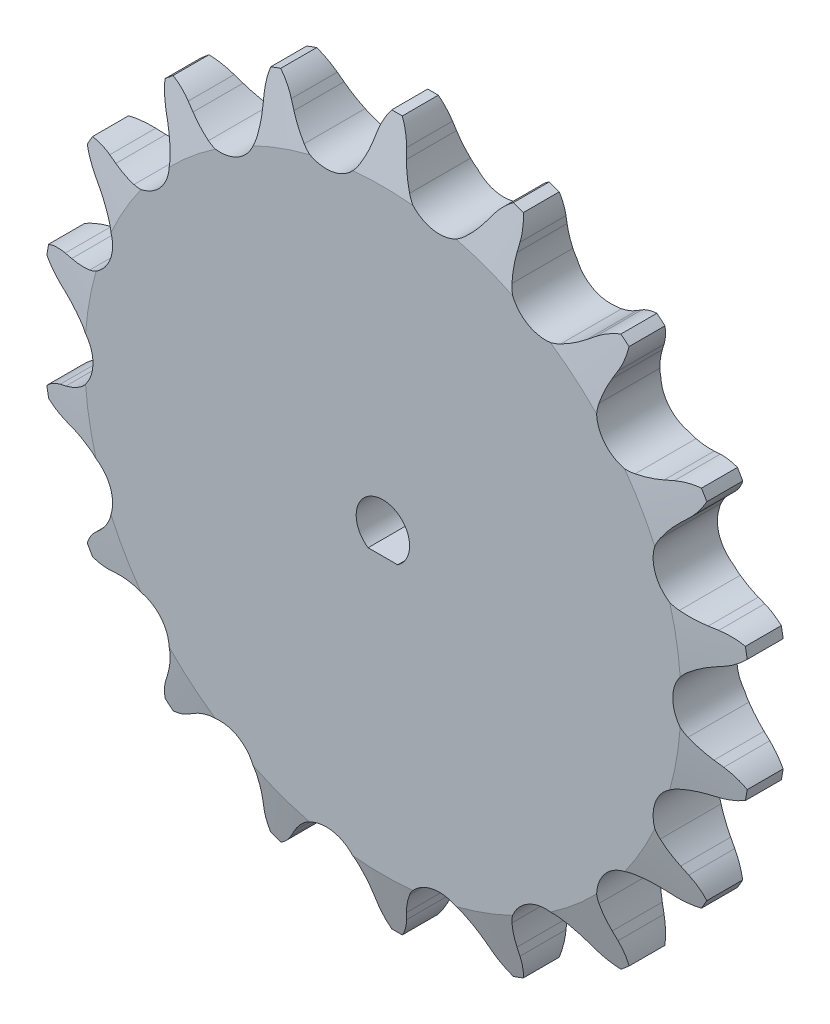
SolidWorks part; units mm, degrees
ref_plane "Front Plane" through (0, 0, 0) normal (0, 0, 1) x (1, 0, 0)
ref_plane "Top Plane" through (0, 0, 0) normal (0, 1, 0) x (1, 0, 0)
ref_plane "Right Plane" through (0, 0, 0) normal (1, 0, 0) x (0, 0, -1)
sketch "Sketch0" plane through (0, 0, 0) normal (0, 0, 1) x (1, 0, 0)
  line L0 (6.35, -36.0126) -> (0, 0) construction
  line L1 (0, 0) -> (18.2841, -31.669) construction
  line L2 (0, 0) -> (-6.35, -36.0126) construction
  line L3 (6.35, -36.0126) -> (18.2841, -31.669) construction
  line L4 (6.35, -36.0126) -> (-6.35, -36.0126) construction
  line L5 (11.3039, -35.8321) -> (10.78, -35.0389)
  line L6 (6.35, -36.0126) -> (0, -37.1323) construction
  line L7 (1.6331, -37.5373) -> (1.8541, -36.6128)
  line L8 (0, -36.0126) -> (0, -39.8226) construction
  line L9 (9.0227, -33.0094) -> (2.1353, -40.7487) construction
  line L10 (0, 0) -> (0, -36.0126) construction
  line L11 (10.78, -35.0389) -> (2.1353, -40.7487) construction
  line L12 (0, -39.8226) -> (0, -40.5391) construction
  line L13 (16.7756, -32.218) -> (11.3039, -35.8321) construction
  circle A0 centre (0, 0) radius 39.8226 construction
  circle A1 centre (0, 0) radius 36.5682 construction
  arc A2 (-5.6013, -42.514) -> (19.8041, -38.0343) centre (0, 0) ccw
  circle A3 centre (0, 0) radius 40.5391 construction
  circle A4 centre (6.35, -36.0126) radius 3.9624 construction
  arc A7 (9.0227, -33.0094) -> (2.8113, -34.1046) centre (6.35, -36.0126) ccw
  circle A8 centre (6.35, -36.0126) radius 4.0203 construction
  arc A9 (11.3039, -35.8321) -> (19.8041, -38.0343) centre (16.7756, -32.218) ccw
  arc A10 (10.78, -35.0389) -> (9.0227, -33.0094) centre (2.1353, -40.7487) ccw
  arc A11 (1.6331, -37.5373) -> (-5.6013, -42.514) centre (-4.7447, -36.0126) cw
  arc A12 (1.8541, -36.6128) -> (2.8113, -34.1046) centre (11.9303, -39.0215) cw
  dimension "D1" = 4.0203
  dimension "R" = 4.0203
sketch "Sketch1" plane through (0, 0, 0) normal (1, 0, 0) x (0, 0, -1)
  line L0 (3.6068, 0) -> (-3.6068, 0)
  line L1 (-3.6068, 0) -> (-3.6068, 33.4726)
  line L2 (-3.6068, 33.4726) -> (-2.0193, 39.8226)
  line L3 (-2.0193, 39.8226) -> (2.0193, 39.8226)
  line L4 (2.0193, 39.8226) -> (3.6068, 33.4726)
  line L5 (3.6068, 33.4726) -> (3.6068, 0)
  line L7 (0, 39.8226) -> (0, 0) construction
  line L8 (-3.6068, 33.4726) -> (3.6068, 33.4726) construction
  line L9 (0, 39.8226) -> (0, -39.8226) construction
  line L10 (-3.6068, 33.4726) -> (-3.6068, 39.8226) construction
  line L11 (-3.6068, 39.8226) -> (-2.0193, 39.8226) construction
  line L12 (2.0193, 39.8226) -> (3.6068, 39.8226) construction
  line L13 (3.6068, 39.8226) -> (3.6068, 33.4726) construction
revolve "Revolve1" add sketch "Sketch1" angle 360 mid plane about L0
extrude "Cut-Extrude1" cut sketch "Sketch0" against normal through all and the other way through all
pattern_circular "CirPattern1" count 18 over 360 about axis through (0, 0, 0) along (0, 0, 1) of "Cut-Extrude1"
sketch "Sketch2" plane through (0, 0, 0) normal (0, 0, 1) x (1, 0, 0)
  circle A0 centre (0, 0) radius 7.9375 construction
  circle A1 centre (0, 0) radius 30.1625
  circle A2 centre (0, 0) radius 39.878 construction
  dimension "Bore" = 15.875
  dimension "Hub Dia." = 60.325
  dimension "OD" = 79.756
sketch "Sketch3" plane through (0, 0, 0) normal (0, 0, 1) x (1, 0, 0)
  line L0 (-1.6583, -2.5) -> (1.6583, -2.5)
  arc A1 (1.6583, -2.5) -> (-1.6583, -2.5) centre (0, 0) ccw
  circle A2 centre (0, 0) radius 39.878 construction
  circle A3 centre (0, 0) radius 39.878
  dimension "D1" = 6
  dimension "D2" = 2.5
extrude "Cut-Extrude2" cut sketch "Sketch3" along normal through all and the other way through all flip side to cut
equation "\"360/N@Sketch0\" = 360/\"Teeth@CirPattern1\""
equation "\"Ds@Sketch0\" = 1.005 * \"Dr@Sketch0\" + 0.003"
equation "\"R@Sketch0\" = 1/2 * \"Ds@Sketch0\""
equation "\"A@Sketch0\" = 35 +  ( 60 / \"Teeth@CirPattern1\" ) "
equation "\"B@Sketch0\" = 18 -  ( 56 / \"Teeth@CirPattern1\" )"
equation "\"ac@Sketch0\" = 0.8 * \"Dr@Sketch0\""
equation "\"ab@Sketch0\" = 1.4 * \"Dr@Sketch0\""
equation "\"J@Sketch0\" = 0.3 * \"Pitch@Sketch0\""
equation "\"h@Sketch1\" = \"Pitch@Sketch0\" / 2"
equation "\"g@Sketch1\" = \"h@Sketch1\" / 4"
